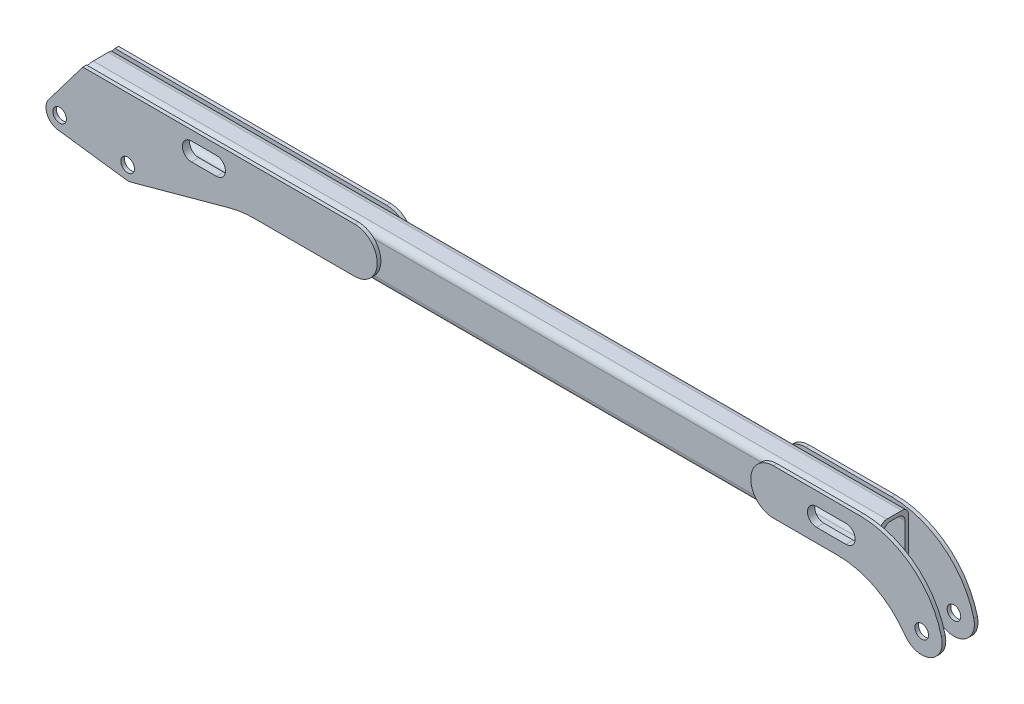
SolidWorks part; units mm, degrees
ref_plane "Front Plane" through (0, 0, 0) normal (0, 0, 1) x (1, 0, 0)
ref_plane "Top Plane" through (0, 0, 0) normal (0, 1, 0) x (1, 0, 0)
ref_plane "Right Plane" through (0, 0, 0) normal (1, 0, 0) x (0, 0, -1)
sketch "Sketch1" plane through (0, 0, 0) normal (0, 0, 1) x (1, 0, 0)
  line L0 (-4159.9566, -2833.2558) -> (-8051.9957, -1977.5355) construction
  line L1 (0, 0) -> (3985, 0) construction
  dimension "D1" = 3985
  dimension "D2" = 3985
sketch "Sketch3" plane through (0, 0, 0) normal (1, 0, 0) x (0, 0, -1)
  line L0 (0, 0) -> (0, 191.3847) construction
  line L1 (-23.5, 109.5) -> (23.5, 109.5)
  line L2 (-31.5, 117.5) -> (31.5, 117.5)
  line L3 (-31.5, 117.5) -> (-31.5, 17.5)
  line L4 (-31.5, 17.5) -> (31.5, 17.5)
  line L5 (31.5, 117.5) -> (31.5, 17.5)
  line L6 (-31.5, 117.5) -> (31.5, 17.5) construction
  line L7 (-31.5, 17.5) -> (31.5, 117.5) construction
  line L8 (23.5, 109.5) -> (23.5, 25.5)
  line L9 (-23.5, 25.5) -> (23.5, 25.5)
  line L10 (-23.5, 109.5) -> (-23.5, 25.5)
  point P3 (0, 67.5)
  dimension "D1" = 100
  dimension "D2" = 63
  dimension "D4" = 17.5
  dimension "D3" = 8
extrude "Boss-Extrude1" add sketch "Sketch3" along normal blind 1800
fillet "Fillet1" radius 15 8 edges at (900, 17.5, -31.5) (900, 25.5, 23.5) (900, 109.5, 23.5) (900, 109.5, -23.5) (900, 25.5, -23.5) (900, 17.5, 31.5) (900, 117.5, -31.5) (900, 117.5, 31.5)
sketch "Sketch4" plane through (0, 0, 31.5) normal (0, 0, 1) x (1, 0, 0)
  line L0 (51.1325, 117.5) -> (-23.9412, 18.0781)
  line L1 (146.0351, -49.7368) -> (-3.9649, -29.7368)
  line L2 (375.313, 10.4345) -> (157.9036, -48.9402)
  line L3 (51.1325, 117.5) -> (650, 117.5)
  line L5 (650, 17.5) -> (428.0035, 17.5)
  circle A0 centre (0, 0) radius 15
  circle A1 centre (150, -20) radius 15
  arc A2 (-23.9412, 18.0781) -> (-3.9649, -29.7368) centre (0, 0) ccw
  arc A3 (146.0351, -49.7368) -> (157.9036, -48.9402) centre (150, -20) ccw
  arc A4 (650, 17.5) -> (650, 117.5) centre (650, 67.5) ccw
  arc A5 (375.313, 10.4345) -> (428.0035, 17.5) centre (428.0035, -182.5) cw
  point P21 (870.3716, 67.5)
  point P22 (649.1356, 67.5)
  point P23 (-63.2346, 117.5)
  dimension "D1" = 30
  dimension "D2" = 30
  dimension "D3" = 150
  dimension "D5" = 60
  dimension "D6" = 60
  dimension "D7" = 100
  dimension "D9" = 200
  dimension "D4" = 20
  dimension "D8" = 650
extrude "Boss-Extrude2" add sketch "Sketch4" along normal blind 8
mirror "Mirror2" about plane through (0, 0, 0) normal (0, 0, 1) of "Boss-Extrude2"
sketch "Sketch5" plane through (0, 0, 39.5) normal (0, 0, 1) x (1, 0, 0)
  line L0 (290.508, 76.142) -> (345.508, 76.142) construction
  line L1 (290.508, 96.142) -> (345.508, 96.142)
  line L2 (290.508, 56.142) -> (345.508, 56.142)
  line L3 (0, 76.142) -> (592.2563, 76.142) construction
  line L4 (0, 102.5) -> (0, 49.784) construction
  arc A0 (290.508, 96.142) -> (290.508, 56.142) centre (290.508, 76.142) ccw
  arc A1 (345.508, 56.142) -> (345.508, 96.142) centre (345.508, 76.142) ccw
  point P2 (318.008, 76.142)
  point P11 (290.508, 67.5)
  dimension "D1" = 20
  dimension "D2" = 55
extrude "Cut-Extrude3" cut sketch "Sketch5" against normal through all
sketch "Sketch6" plane through (0, 0, 31.5) normal (0, 0, 1) x (1, 0, 0)
  line L0 (51.1325, 117.5) -> (-2.7942, 46.0836)
  line L1 (51.1325, 117.5) -> (-23.9412, 18.0781) construction
  line L2 (-2.7942, 46.0836) -> (-2.7942, 117.5)
  line L3 (-2.7942, 117.5) -> (51.1325, 117.5)
sketch "Sketch7" plane through (0, 0, 31.5) normal (0, 0, 1) x (1, 0, 0)
  line L0 (0, 17.5) -> (51.1325, 117.5)
  line L1 (51.1325, 117.5) -> (-2.7942, 117.5)
  line L2 (-2.7942, 117.5) -> (-2.7942, 17.5)
  line L3 (-2.7942, 17.5) -> (0, 17.5)
extrude "Cut-Extrude5" cut sketch "Sketch7" against normal up to surface (63 mm away) up to face at (357.0392, 110.8994, -31.5)
sketch "Sketch8" plane through (0, 0, 31.5) normal (0, 0, 1) x (1, 0, 0)
  line L0 (51.1325, 117.5) -> (1800, 117.5) construction
  line L1 (1573.2088, 17.5) -> (1714.6781, 17.5)
  line L2 (1573.2088, 117.5) -> (1763.0512, 117.5)
  arc A1 (1862.9149, -60.4891) -> (1943.7125, -24.3128) centre (1900, -35) ccw
  arc A2 (1573.2088, 117.5) -> (1573.2088, 17.5) centre (1573.2088, 67.5) ccw
  arc A3 (1714.6781, 17.5) -> (1862.9149, -60.4891) centre (1714.6781, -162.3742) cw
  arc A4 (1763.0512, 117.5) -> (1943.7125, -24.3128) centre (1763.0512, -68.4824) cw
  circle A5 centre (1900, -35) radius 15
  dimension "D1" = 100
  dimension "D2" = 90
  dimension "D4" = 30
  dimension "D3" = 1900
  dimension "D5" = 35
extrude "Boss-Extrude3" add sketch "Sketch8" along normal blind 8
mirror "Mirror8" about plane through (0, 0, 0) normal (0, 0, 1) of "Boss-Extrude3"
sketch "Sketch9" plane through (0, 0, 39.5) normal (0, 0, 1) x (1, 0, 0)
  line L0 (1573.2088, 67.5) -> (1798.7504, 67.5) construction
  line L1 (1668.1982, 67.5) -> (1733.1982, 67.5) construction
  line L2 (1668.1982, 87.5) -> (1733.1982, 87.5)
  line L3 (1668.1982, 47.5) -> (1733.1982, 47.5)
  arc A0 (1668.1982, 87.5) -> (1668.1982, 47.5) centre (1668.1982, 67.5) ccw
  arc A1 (1733.1982, 47.5) -> (1733.1982, 87.5) centre (1733.1982, 67.5) ccw
  point P5 (1700.6982, 67.5)
  point P10 (1667.4168, 67.5)
  dimension "D1" = 20
  dimension "D2" = 65
extrude "Cut-Extrude6" cut sketch "Sketch9" against normal through all
